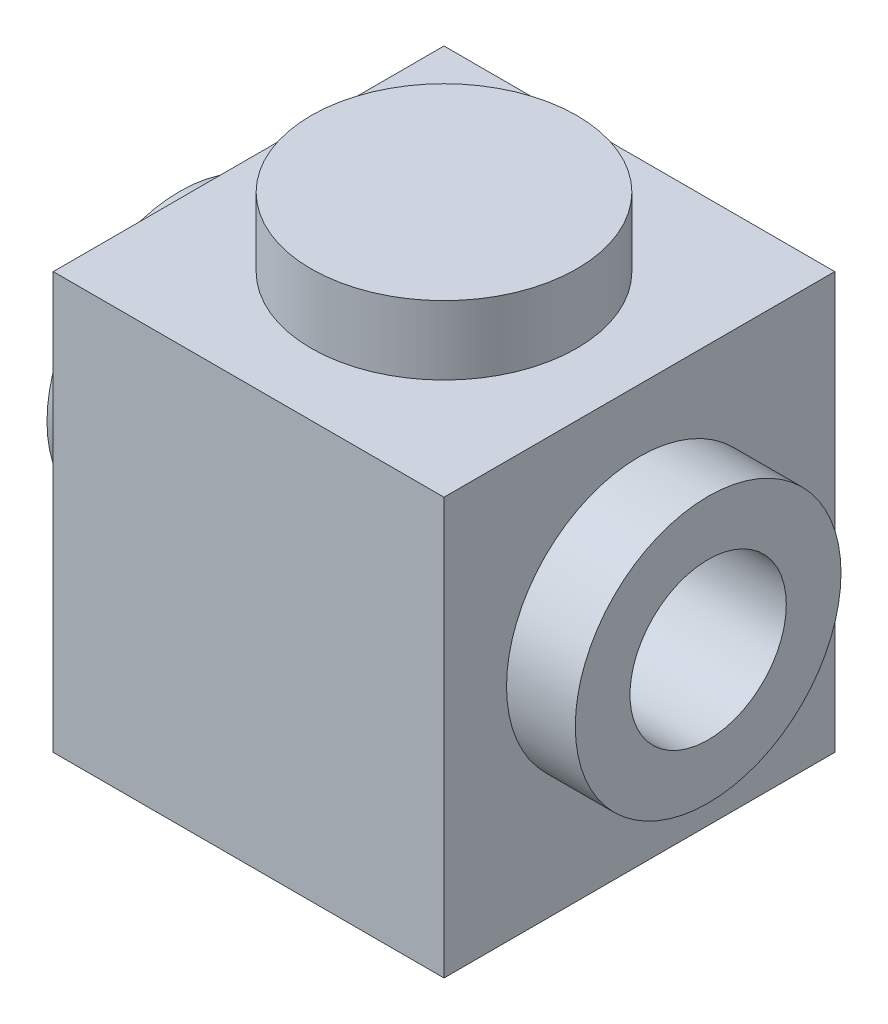
SolidWorks part; units mm, degrees
material "ABS"
ref_plane "Front Plane" through (0, 0, 0) normal (0, 0, 1) x (1, 0, 0)
ref_plane "Top Plane" through (0, 0, 0) normal (0, 1, 0) x (1, 0, 0)
ref_plane "Right Plane" through (0, 0, 0) normal (1, 0, 0) x (0, 0, -1)
sketch "Sketch1" plane through (0, 0, 0) normal (0, 1, 0) x (1, 0, 0)
  line L1 (-3.9688, 3.9688) -> (3.9688, 3.9688)
  line L2 (-3.9688, 3.9688) -> (-3.9688, -3.9687)
  line L3 (-3.9688, -3.9687) -> (3.9688, -3.9687)
  line L4 (3.9688, 3.9688) -> (3.9688, -3.9687)
  line L5 (-3.9688, 3.9688) -> (3.9688, -3.9687) construction
  line L6 (-3.9688, -3.9687) -> (3.9688, 3.9688) construction
  point P0 (0, 0)
  dimension "D1" = 7.9375
  dimension "D2" = 7.9375
extrude "Boss-Extrude1" add sketch "Sketch1" along normal mid plane 8.4582
sketch "Sketch2" plane through (0, -4.2291, 0) normal (0, -1, 0) x (1, 0, 0)
  line L12 (2.6987, -2.6988) -> (2.6987, 2.6987)
  line L13 (2.6987, 2.6987) -> (-2.6987, 2.6987)
  line L14 (-2.6987, 2.6987) -> (-2.6987, -2.6988)
  line L15 (-2.6987, -2.6988) -> (2.6987, -2.6988)
  line L16 (2.6987, -2.6988) -> (2.6987, 2.6987)
  line L17 (2.6987, 2.6987) -> (-2.6987, 2.6987)
  line L18 (-2.6987, 2.6987) -> (-2.6987, -2.6988)
  line L19 (-2.6987, -2.6988) -> (2.6987, -2.6988)
  circle A0 centre (0, 0) radius 3.175
  circle A1 centre (0, 0) radius 2.413
  dimension "D2" = 6.35
  dimension "D3" = 0.762
  dimension "D1" = 1.27
extrude "Cut-Extrude1" cut sketch "Sketch2" against normal offset from surface (7.1882 mm away) 1.27 contours A0 L17 L18 | L19 A0 L16 L17 L18 A1 | A1 | A0 L18 L19 | A0 L19 L16 | A0 L16 L17
sketch "Sketch3" plane through (0, 4.2291, 0) normal (0, 1, 0) x (1, 0, 0)
  line L0 (3.9688, -3.9687) -> (3.9688, 3.9688) construction
  line L1 (-3.9688, -3.9687) -> (3.9688, -3.9687) construction
  circle A0 centre (0, 0) radius 2.6987
  dimension "D3" = 5.3975
  dimension "D1" = 3.9688
  dimension "D2" = 3.9688
extrude "Boss-Extrude2" add sketch "Sketch3" along normal blind 1.397
sketch "Sketch5" plane through (3.9688, 0, 0) normal (1, 0, 0) x (0, 0, -1)
  line L0 (-3.9687, 4.2291) -> (3.9688, 4.2291) construction
  line L1 (0, 4.3656) -> (0, -4.3656) construction
  circle A0 centre (0, 0.2604) radius 2.6988
  dimension "D1" = 5.3975
  dimension "D2" = 3.9688
extrude "Boss-Extrude4" add sketch "Sketch5" along normal blind 1.397
mirror "Mirror1" about plane through (0, 0, 0) normal (1, 0, 0) of "Boss-Extrude4"
sketch "Sketch6" plane through (5.3658, 0, 0) normal (1, 0, 0) x (0, 0, -1)
  circle A0 centre (0, 0.2604) radius 2.6988 construction
  circle A1 centre (0, 0.2604) radius 2.6988
  circle A2 centre (0, 0.2604) radius 1.5875
  dimension "D1" = 3.175
extrude "Cut-Extrude2" cut sketch "Sketch6" against normal through all contours A2
